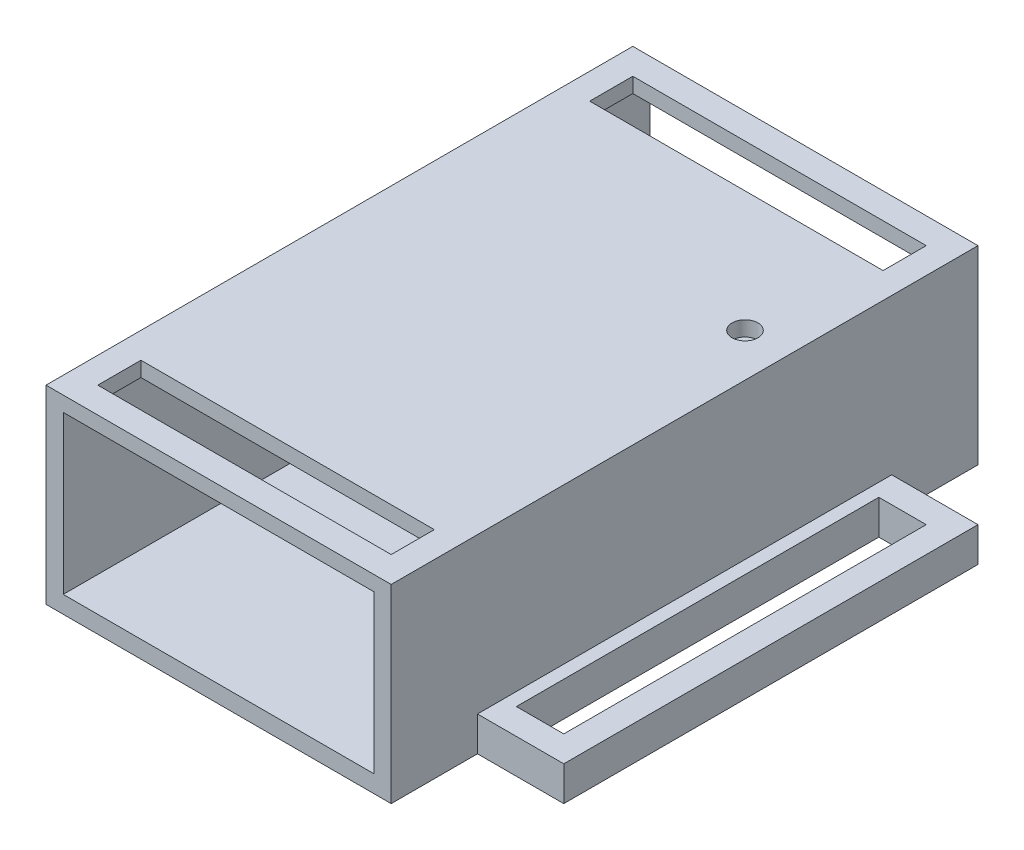
SolidWorks part; units mm, degrees
ref_plane "Front Plane" through (0, 0, 0) normal (0, 0, 1) x (1, 0, 0)
ref_plane "Top Plane" through (0, 0, 0) normal (0, 1, 0) x (1, 0, 0)
ref_plane "Right Plane" through (0, 0, 0) normal (1, 0, 0) x (0, 0, -1)
sketch "Sketch1" plane through (0, 0, 0) normal (0, 1, 0) x (1, 0, 0)
  line L0 (40, 0) -> (40, -22) construction
  line L1 (0, 0) -> (40, 0)
  line L2 (0, 0) -> (0, -68)
  line L3 (0, -68) -> (40, -68)
  line L4 (40, 0) -> (40, -68)
  line L5 (40, -22) -> (35, -22) construction
  circle A0 centre (35, -22) radius 1.5
  dimension "D4" = 5
  dimension "D5" = 3
  dimension "D1" = 68
  dimension "D2" = 40
  dimension "D3" = 22
extrude "Boss-Extrude1" add sketch "Sketch1" along normal blind 22
sketch "Sketch2" plane through (0, 0, 68) normal (0, 0, 1) x (1, 0, 0)
  line L0 (0, 0) -> (0, 2) construction
  line L1 (0, 22) -> (0, 0) construction
  line L2 (0, 2) -> (2, 2) construction
  line L3 (40, 0) -> (40, 2) construction
  line L4 (40, 22) -> (40, 0) construction
  line L5 (40, 2) -> (38, 2) construction
  line L6 (2, 2) -> (38, 2)
  line L7 (38, 2) -> (38, 20.2659)
  line L8 (38, 20.2659) -> (2, 20.2659)
  line L9 (2, 20.2659) -> (2, 2)
  dimension "D1" = 2
  dimension "D2" = 2
  dimension "D3" = 2
extrude "Cut-Extrude1" cut sketch "Sketch2" against normal through all
sketch "Sketch3" plane through (0, 22, 0) normal (0, 1, 0) x (1, 0, 0)
  line L0 (0, -68) -> (0, -65) construction
  line L1 (0, 0) -> (0, -68) construction
  line L2 (0, -65) -> (3, -65) construction
  line L3 (37, -65) -> (3, -65)
  line L4 (3, -60) -> (3, -65)
  line L5 (3, -60) -> (37, -60)
  line L6 (20, -58.9149) -> (20, -65) construction
  line L7 (37, -60) -> (37, -65)
  line L8 (0, -34) -> (40, -34) construction
  line L9 (40, -68) -> (40, 0) construction
  line L10 (37, -8) -> (37, -3)
  line L11 (37, -3) -> (3, -3)
  line L12 (3, -8) -> (3, -3)
  line L13 (3, -8) -> (37, -8)
  point P14 (20, -60)
  dimension "D1" = 3
  dimension "D2" = 3
  dimension "D3" = 5
extrude "Cut-Extrude2" cut sketch "Sketch3" against normal blind 2
sketch "Sketch6" plane through (40, 0, 0) normal (1, 0, 0) x (0, 0, -1)
  line L0 (-68, 0) -> (-58, 0) construction
  line L1 (-68, 0) -> (0, 0) construction
  line L2 (-58, 0) -> (-58, 4) construction
  line L3 (0, 0) -> (-10, 0) construction
  line L4 (-10, 0) -> (-10, 4) construction
  line L6 (-58, 4) -> (-10, 4)
  line L7 (-58, 4) -> (-58, 0)
  line L8 (-58, 0) -> (-10, 0)
  line L9 (-10, 4) -> (-10, 0)
  dimension "D1" = 10
  dimension "D2" = 4
  dimension "D3" = 10
extrude "Boss-Extrude3" add sketch "Sketch6" along normal blind 10
sketch "Sketch7" plane through (0, 4, 0) normal (0, 1, 0) x (1, 0, 0)
  line L0 (50, -10) -> (50, -58) construction
  line L1 (41.5091, -13) -> (47, -13)
  line L2 (41.5091, -13) -> (41.5091, -55)
  line L3 (41.5091, -55) -> (47, -55)
  line L4 (47, -13) -> (47, -55)
  line L5 (50, -10) -> (40, -10) construction
  line L6 (50, -58) -> (40, -58) construction
  point P8 (45, -58)
  dimension "D1" = 3
  dimension "D2" = 3
  dimension "D3" = 3
extrude "Cut-Extrude4" cut sketch "Sketch7" against normal blind 10
ref_plane "Plane1" through (20, 0, 0) normal (1, 0, 0) x (0, 0, -1)
mirror "Mirror1" about plane through (20, 0, 0) normal (1, 0, 0) of "Boss-Extrude3"
mirror "Mirror2" about plane through (20, 0, 0) normal (1, 0, 0) of "Cut-Extrude4"
